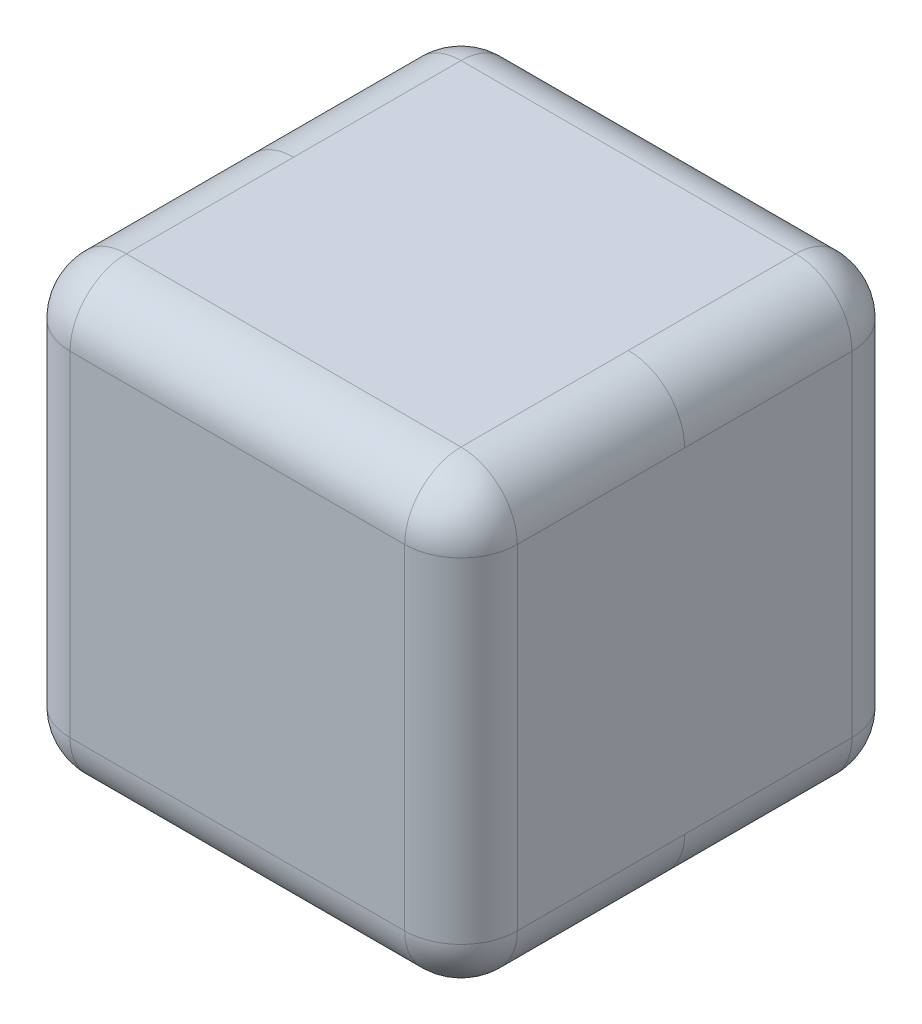
SolidWorks part; units mm, degrees
ref_plane "Front Plane" through (0, 0, 0) normal (0, 0, 1) x (1, 0, 0)
ref_plane "Top Plane" through (0, 0, 0) normal (0, 1, 0) x (1, 0, 0)
ref_plane "Right Plane" through (0, 0, 0) normal (1, 0, 0) x (0, 0, -1)
sketch "Sketch1" plane through (0, 0, 0) normal (0, 1, 0) x (1, 0, 0)
  line L0 (0, 73.5) -> (0, 0) construction
  line L1 (-73.5, 73.5) -> (73.5, 73.5)
  line L2 (-73.5, 73.5) -> (-73.5, 0)
  line L3 (-73.5, 0) -> (73.5, 0)
  line L4 (73.5, 73.5) -> (73.5, 0)
  point P7 (0, 73.5)
  dimension "D1" = 73.5
  dimension "D2" = 147
extrude "Boss-Extrude1" add sketch "Sketch1" along normal blind 147
fillet "Fillet1" radius 18.5 8 edges at (0, 0, -73.5) (73.5, 73.5, -73.5) (73.5, 0, -36.75) (-73.5, 73.5, -73.5) (-73.5, 0, -36.75) (0, 147, -73.5) (73.5, 147, -36.75) (-73.5, 147, -36.75)
sketch "Sketch2" plane through (0, 0, 0) normal (0, 0, 1) x (1, 0, 0)
  line L0 (0, 137) -> (0, 2) construction
  line L1 (-50, 137) -> (50, 137)
  line L2 (-50, 137) -> (-50, 2)
  line L3 (-50, 2) -> (50, 2)
  line L4 (50, 137) -> (50, 2)
  line L5 (-73.5, 0) -> (73.5, 0) construction
  dimension "D1" = 100
  dimension "D2" = 135
  dimension "D3" = 2
extrude "Cut-Extrude1" cut sketch "Sketch2" against normal blind 50
fillet "Fillet2" radius 20 8 edges at (0, 137, -50) (50, 69.5, -50) (0, 2, -50) (-50, 69.5, -50) (-50, 2, -25) (50, 2, -25) (50, 137, -25) (-50, 137, -25)
mirror "Mirror1" about plane through (-73.5, 147, 0) normal (0, 0, -1) of "Fillet2", "Cut-Extrude1", "Boss-Extrude1", "Fillet1"
